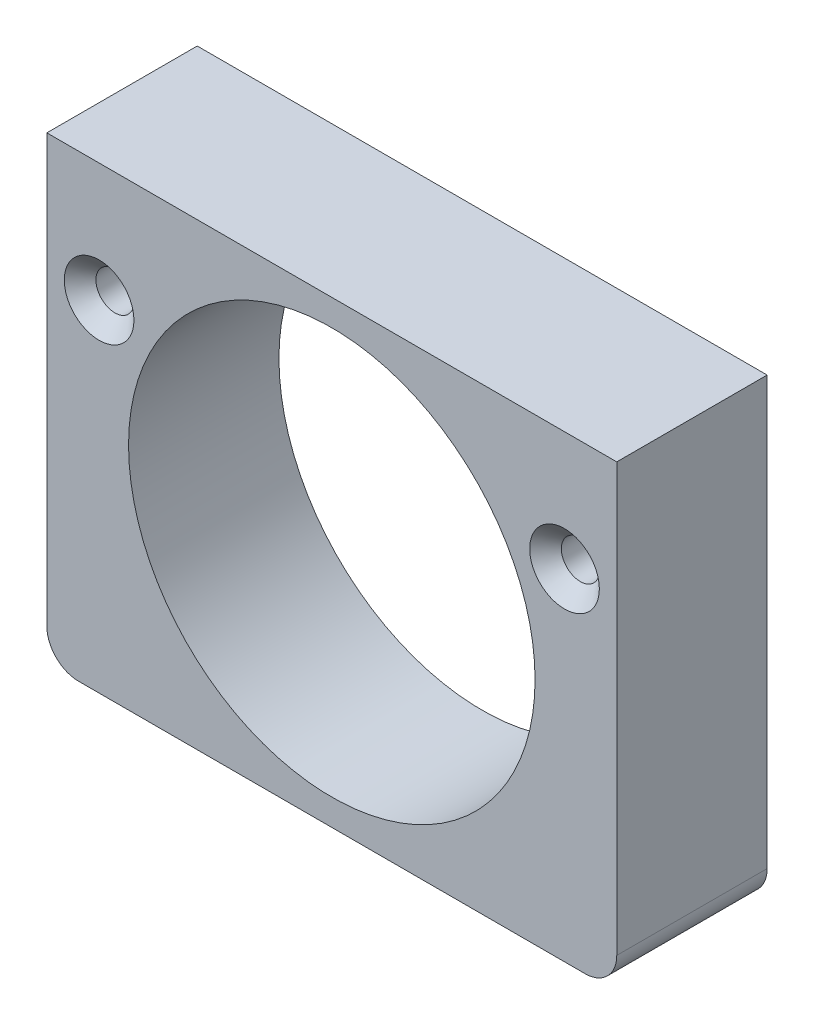
SolidWorks part; units mm, degrees
ref_plane "Front Plane" through (0, 0, 0) normal (0, 0, 1) x (1, 0, 0)
ref_plane "Top Plane" through (0, 0, 0) normal (0, 1, 0) x (1, 0, 0)
ref_plane "Right Plane" through (0, 0, 0) normal (1, 0, 0) x (0, 0, -1)
sketch "Sketch1" plane through (0, 0, 0) normal (0, 0, 1) x (1, 0, 0)
  line L1 (-16, -14.5) -> (16, -14.5)
  line L2 (-18, -12.5) -> (-18, 14.5)
  line L3 (-18, 14.5) -> (18, 14.5)
  line L4 (18, -12.5) -> (18, 14.5)
  line L5 (-18, -14.5) -> (18, 14.5) construction
  line L6 (-18, 14.5) -> (18, -14.5) construction
  arc A0 (16, -14.5) -> (18, -12.5) centre (16, -12.5) ccw
  arc A1 (-16, -14.5) -> (-18, -12.5) centre (-16, -12.5) cw
  point P0 (0, 0)
  dimension "D1" = 2
  dimension "D2" = 29
  dimension "D3" = 36
extrude "Boss-Extrude1" add sketch "Sketch1" along normal blind 9.5
ref_plane "Plane1" through (0, 0, 9.5) normal (0, 0, 1) x (0, 1, 0)
sketch "Sketch2" plane through (0, 0, 9.5) normal (0, 0, 1) x (0, 1, 0)
  circle A0 centre (0, 0) radius 12.8397
  dimension "D1" = 25.6794
extrude "Cut-Extrude1" cut sketch "Sketch2" against normal up to next
hole_wizard "CSK for M2 Countersunk Flat Head Screw1" positions "Sketch4" profile "Sketch5" countersink size "M2" standard "DIN" end condition up to next
sketch "Sketch4" plane through (0, 0, 9.5) normal (0, 0, 1) x (1, 0, 0)
  line L0 (18, 14.5) -> (-18, 14.5) construction
  line L1 (18, -12.5) -> (18, 14.5) construction
  line L2 (-18, 14.5) -> (-18, -12.5) construction
  point P0 (-14.7, 7)
  point P2 (14.7, 7)
  dimension "D1" = 7.5
  dimension "D2" = 3.3
  dimension "D3" = 3.3
sketch "Sketch5" plane through (-14.7, 7, 9.5) normal (1, 0, 0) x (0, -1, 0)
  line L0 (0, 0) -> (0, 9.5)
  line L1 (0, 9.5) -> (1.2, 9.5)
  line L2 (1.2, 9.5) -> (1.2, 1)
  line L3 (1.2, 1) -> (2.2, 0)
  line L5 (2.2, 0) -> (0, 0)
  line L6 (-1.2, 1) -> (-2.2, 0) construction
  line L11 (0, -6.35) -> (0, 107.95) construction
  dimension "Thru Hole Dia." = 2.4
  dimension "Thru Hole Depth" = 9.5
  dimension "Near C'Sink Dia." = 4.4
  dimension "Near C'Sink Angle" = 90
